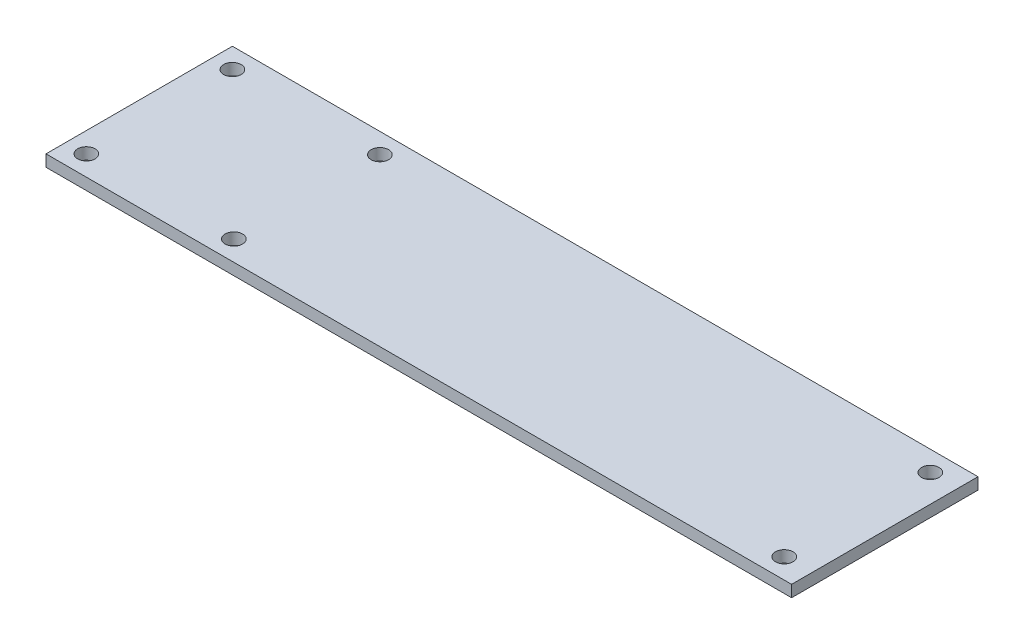
SolidWorks part; units mm, degrees
ref_plane "Alzado" through (0, 0, 0) normal (0, 0, 1) x (1, 0, 0)
ref_plane "Planta" through (0, 0, 0) normal (0, 1, 0) x (1, 0, 0)
ref_plane "Vista lateral" through (0, 0, 0) normal (1, 0, 0) x (0, 0, -1)
sketch "Croquis2" plane through (0, 0, 0) normal (0, 1, 0) x (1, 0, 0)
  line L1 (-203.2, -50.8) -> (203.2, -50.8)
  line L2 (-203.2, -50.8) -> (-203.2, 50.8)
  line L3 (-203.2, 50.8) -> (203.2, 50.8)
  line L4 (203.2, -50.8) -> (203.2, 50.8)
  line L5 (-203.2, -50.8) -> (203.2, 50.8) construction
  line L6 (-203.2, 50.8) -> (203.2, -50.8) construction
  point P0 (0, 0)
  dimension "D1" = 406.4
  dimension "D2" = 101.6
extrude "Saliente-Extruir1" add sketch "Croquis2" along normal blind 6.35
sketch "Croquis4" plane through (0, 6.35, 0) normal (0, 1, 0) x (1, 0, 0)
  line L0 (-192.2, 39.8) -> (-111.81, 39.8) construction
  line L1 (0, 0) -> (0, 50.8) construction
  line L2 (203.2, 50.8) -> (-203.2, 50.8) construction
  line L3 (0, 0) -> (-203.2, 0) construction
  line L4 (-203.2, 50.8) -> (-203.2, -50.8) construction
  line L6 (203.2, -50.8) -> (203.2, 50.8) construction
  line L7 (-203.2, -50.8) -> (203.2, -50.8) construction
  circle A0 centre (-192.2, 39.8) radius 4.7625
  circle A1 centre (188.2, 39.8) radius 4.7625
  circle A2 centre (188.2, -39.8) radius 4.7625
  circle A3 centre (-192.2, -39.8) radius 4.7625
  circle A4 centre (-111.81, 39.8) radius 4.7625
  circle A5 centre (-111.81, -39.8) radius 4.7625
  dimension "D1" = 9.525
  dimension "D2" = 11
  dimension "D3" = 11
  dimension "D4" = 80.39
  dimension "D5" = 9.525
  dimension "D6" = 9.525
  dimension "D7" = 11
  dimension "D8" = 15
  dimension "D9" = 9.525
  dimension "D10" = 11
  dimension "D11" = 15
extrude "Cortar-Extruir2" cut sketch "Croquis4" against normal blind 6.35
